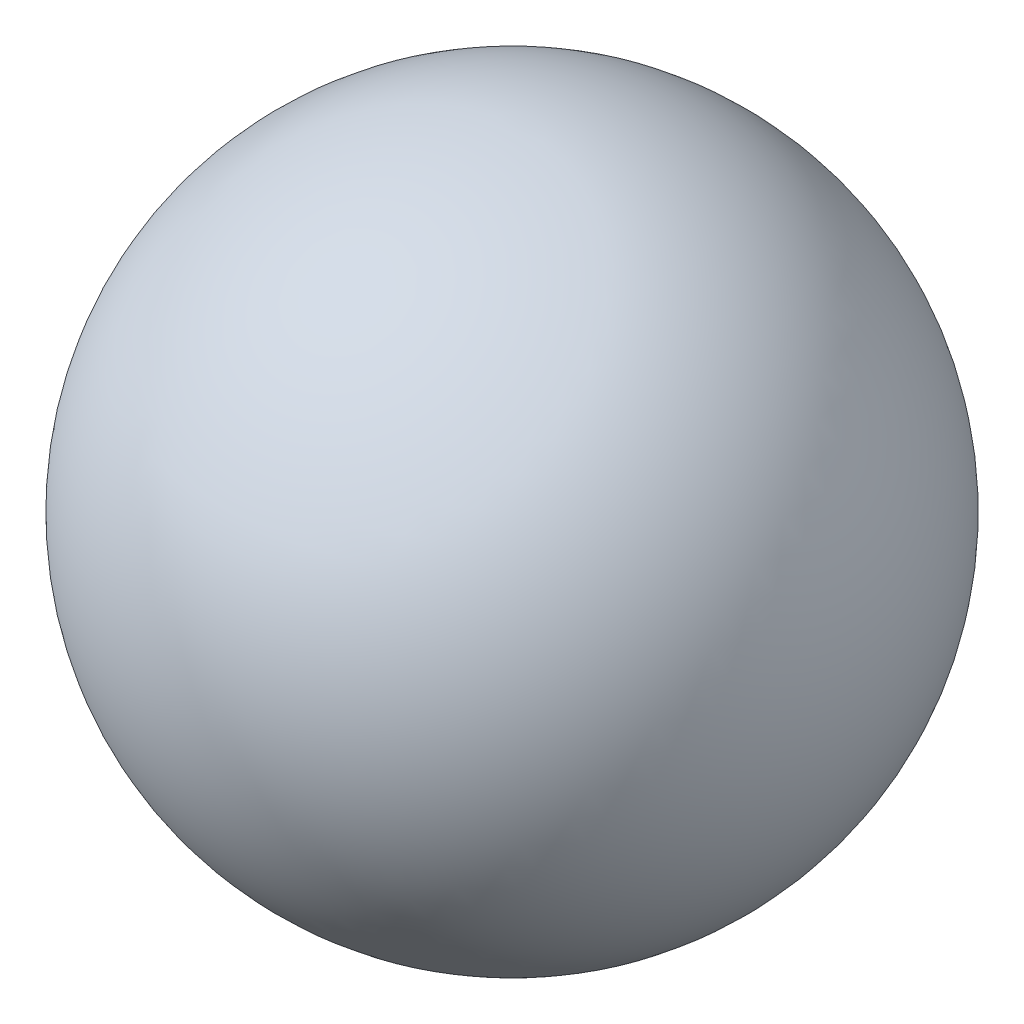
SolidWorks part; units mm, degrees
ref_plane "Front Plane" through (0, 0, 0) normal (0, 0, 1) x (1, 0, 0)
ref_plane "Top Plane" through (0, 0, 0) normal (0, 1, 0) x (1, 0, 0)
ref_plane "Right Plane" through (0, 0, 0) normal (1, 0, 0) x (0, 0, -1)
sketch "Sketch1" plane through (0, 0, 0) normal (0, 0, 1) x (1, 0, 0)
  line L0 (0, 1.995) -> (0, -1.995)
  circle A0 centre (0, 0) radius 1.995 construction
  arc A1 (0, 1.995) -> (0, -1.995) centre (0, 0) cw
  dimension "D1" = 3.99
revolve "Revolve1" add sketch "Sketch1" angle 360 about L0
